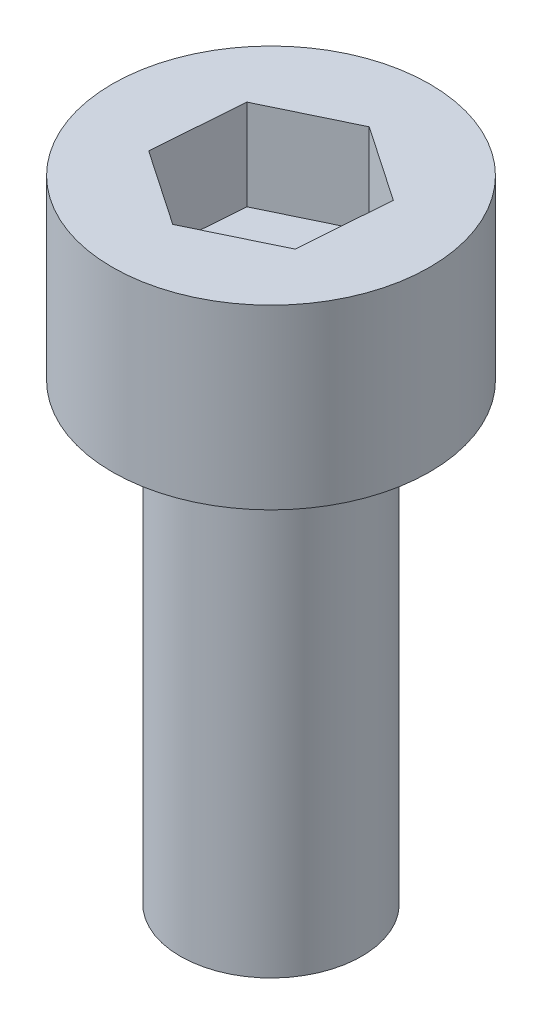
SolidWorks part; units mm, degrees
ref_plane "前视基准面" through (0, 0, 0) normal (0, 0, 1) x (1, 0, 0)
ref_plane "上视基准面" through (0, 0, 0) normal (0, 1, 0) x (1, 0, 0)
ref_plane "右视基准面" through (0, 0, 0) normal (1, 0, 0) x (0, 0, -1)
sketch "草图1" plane through (0, 0, 0) normal (0, 1, 0) x (1, 0, 0)
  circle A0 centre (0, 0) radius 2
  dimension "D1" = 4
extrude "凸台-拉伸1" add sketch "草图1" along normal blind 10
sketch "草图2" plane through (0, 10, 0) normal (0, 1, 0) x (1, 0, 0)
  circle A0 centre (0, 0) radius 3.5
  dimension "D1" = 7
extrude "凸台-拉伸2" add sketch "草图2" along normal blind 3.91
sketch "草图3" plane through (0, 13.91, 0) normal (0, 1, 0) x (1, 0, 0)
  line L1 (1.6694, -1.1386) -> (1.8208, 0.8764)
  line L2 (1.8208, 0.8764) -> (0.1514, 2.015)
  line L3 (0.1514, 2.015) -> (-1.6694, 1.1386)
  line L4 (-1.6694, 1.1386) -> (-1.8208, -0.8764)
  line L5 (-1.8208, -0.8764) -> (-0.1514, -2.015)
  line L6 (-0.1514, -2.015) -> (1.6694, -1.1386)
  circle A0 centre (0, 0) radius 1.75 construction
  dimension "D1" = 3.5
extrude "切除-拉伸1" cut sketch "草图3" against normal blind 2
